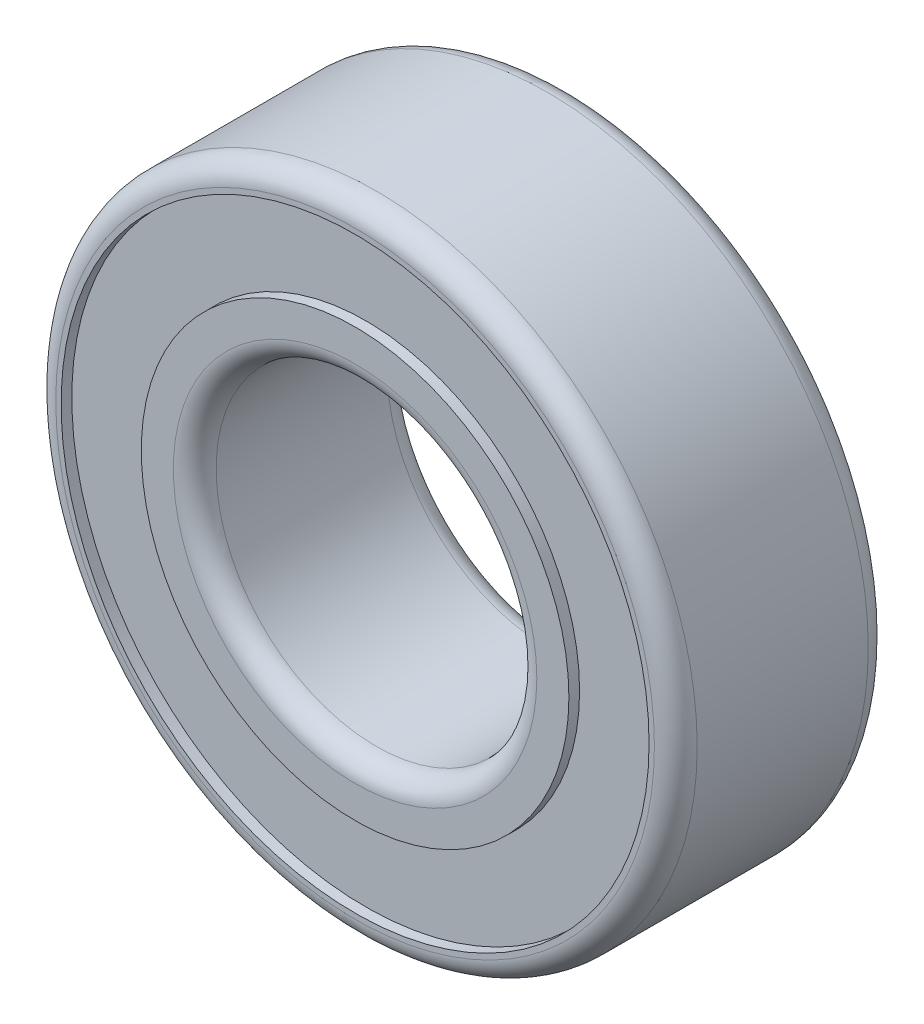
SolidWorks part; units mm, degrees
material "Chrome Stainless Steel"
ref_plane "Front Plane" through (0, 0, 0) normal (0, 0, 1) x (1, 0, 0)
ref_plane "Top Plane" through (0, 0, 0) normal (0, 1, 0) x (1, 0, 0)
ref_plane "Right Plane" through (0, 0, 0) normal (1, 0, 0) x (0, 0, -1)
sketch "Sketch1" plane through (0, 0, 0) normal (0, 0, 1) x (1, 0, 0)
  circle A0 centre (0, 0) radius 3
  circle A1 centre (0, 0) radius 6
  dimension "D1" = 12
  dimension "D2" = 6
extrude "Boss-Extrude1" add sketch "Sketch1" along normal mid plane 4
sketch "Sketch2" plane through (0, 0, 2) normal (0, 0, 1) x (1, 0, 0)
  circle A0 centre (0, 0) radius 4
  circle A1 centre (0, 0) radius 5.5
  dimension "D1" = 8
  dimension "D2" = 11
extrude "Cut-Extrude1" cut sketch "Sketch2" against normal blind 0.2
mirror "Mirror1" about plane through (0, 0, 0) normal (0, 0, 1) of "Cut-Extrude1"
fillet "Fillet1" radius 0.4 4 edges at (3, 0, -2) (3, 0, 2) (6, 0, -2) (6, 0, 2)
